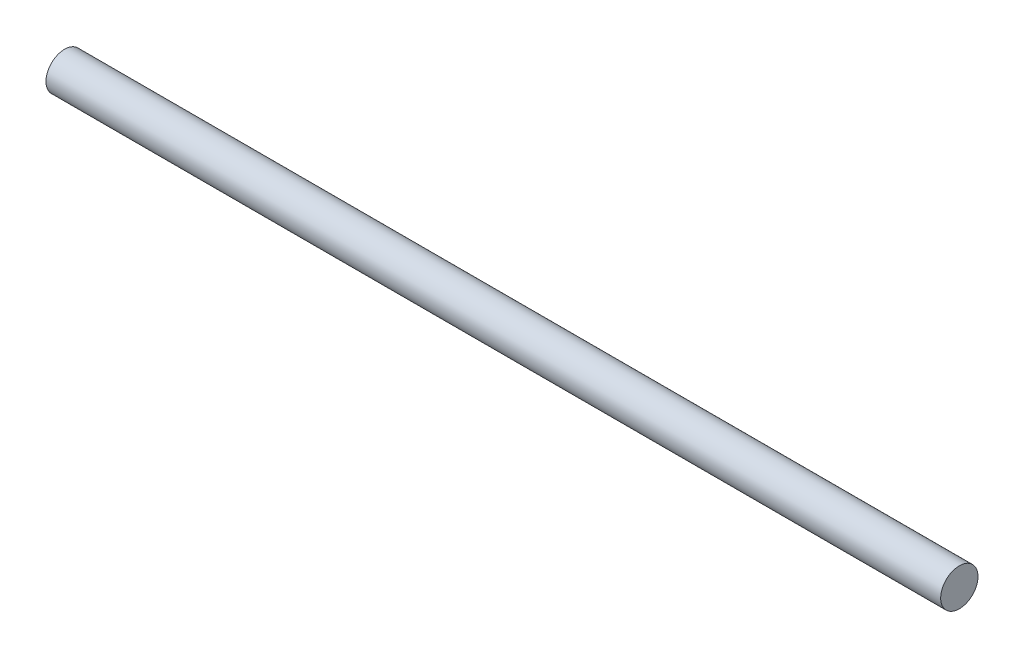
SolidWorks part; units mm, degrees
ref_plane "Front Plane" through (0, 0, 0) normal (0, 0, 1) x (1, 0, 0)
ref_plane "Top Plane" through (0, 0, 0) normal (0, 1, 0) x (1, 0, 0)
ref_plane "Right Plane" through (0, 0, 0) normal (1, 0, 0) x (0, 0, -1)
sketch "Sketch1" plane through (0, 0, 0) normal (1, 0, 0) x (0, 0, -1)
  circle A0 centre (0, 0) radius 19.05
  dimension "D1" = 38.1
extrude "Boss-Extrude1" add sketch "Sketch1" along normal mid plane 913.1
